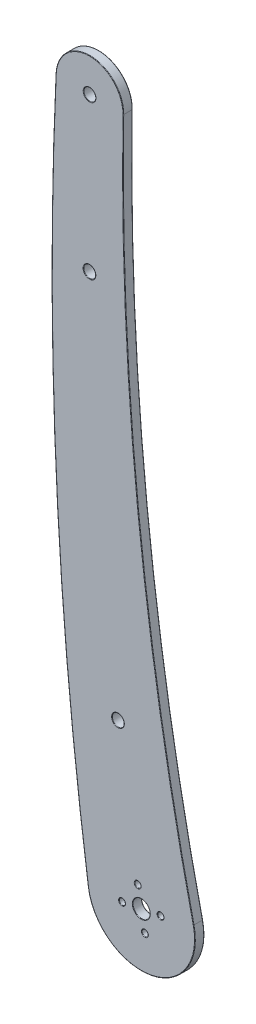
SolidWorks part; units mm, degrees
ref_plane "Front Plane" through (0, 0, 0) normal (0, 0, 1) x (1, 0, 0)
ref_plane "Top Plane" through (0, 0, 0) normal (0, 1, 0) x (1, 0, 0)
ref_plane "Right Plane" through (0, 0, 0) normal (1, 0, 0) x (0, 0, -1)
sketch "Sketch1" plane through (0, 0, 0) normal (0, 0, 1) x (1, 0, 0)
  line L0 (-20.22, 57.58) -> (-37.0777, 278.939) construction
  line L1 (-20.22, 57.58) -> (-37.0777, 278.939) construction
  line L2 (-20.22, 57.58) -> (-17.0242, 40.3743) construction
  line L3 (-20.22, 57.58) -> (-3.0143, 60.7758) construction
  line L4 (-20.22, 57.58) -> (-23.4158, 74.7857) construction
  line L5 (-20.22, 57.58) -> (-37.4257, 54.3842) construction
  circle A0 centre (-37.0777, 278.939) radius 11 construction
  circle A1 centre (-37.0777, 278.939) radius 11 construction
  circle A2 centre (-20.22, 57.58) radius 17.5 construction
  circle A3 centre (-20.22, 57.58) radius 17.5 construction
  circle A4 centre (-20.22, 57.58) radius 2.8
  circle A5 centre (-37.0777, 278.939) radius 1.95
  arc A8 (-26.0792, 278.7566) -> (-3.1679, 61.514) centre (873.7971, 263.8316) ccw
  arc A9 (-48.0656, 279.4542) -> (-37.5474, 55.1282) centre (1150.6174, 223.2484) ccw
  arc A10 (-37.0777, 278.939) -> (-20.22, 57.58) centre (1087.6295, 253.27) ccw construction
  arc A11 (-48.0656, 279.4542) -> (-26.0792, 278.7566) centre (-37.0777, 278.939) cw
  arc A12 (-37.5474, 55.1282) -> (-3.1679, 61.514) centre (-20.22, 57.58) ccw
  circle A13 centre (-37.1074, 228.939) radius 1.95
  circle A15 centre (-27.821, 106.9989) radius 1.95
  circle A17 centre (-19.0531, 51.2975) radius 1
  circle A18 centre (-26.5025, 56.4131) radius 1
  circle A19 centre (-21.3869, 63.8625) radius 1
  circle A20 centre (-13.9375, 58.7469) radius 1
  point P19 (-37.1074, 228.939)
  point P20 (-27.821, 106.9989)
  point P33 (0, 0)
  dimension "D1" = 3.9
  dimension "D2" = 5.6
  dimension "D3" = 1200
  dimension "D4" = 1125
  dimension "D5" = 900
  dimension "D8" = 3.9
  dimension "D9" = 2
  dimension "D6" = 50
  dimension "D7" = 50
  dimension "D10" = 6.39
  dimension "D11" = 6.39
extrude "Boss-Extrude1" add sketch "Sketch1" against normal blind 3
fillet "Fillet1" radius 0.15 24 edges at (-48.0657, 167.0447, -3) (-17.0242, 40.3743, -3) (-21.2391, 169.4376, -3) (-36.7288, 289.9335, -3) (-17.42, 57.58, -3) (-35.1277, 278.939, -3) (-25.871, 106.9989, -3) (-35.1574, 228.939, -3) (-21.2391, 169.4376, 0) (-17.0242, 40.3743, 0) (-48.0657, 167.0447, 0) (-36.7288, 289.9335, 0) (-17.42, 57.58, 0) (-35.1277, 278.939, 0) (-25.871, 106.9989, 0) (-35.1574, 228.939, 0) (-18.0531, 51.2975, -3) (-18.0531, 51.2975, 0) (-25.5025, 56.4131, -3) (-25.5025, 56.4131, 0) (-22.3869, 63.8625, -3) (-14.9375, 58.7469, -3) (-22.3869, 63.8625, 0) (-14.9375, 58.7469, 0)
